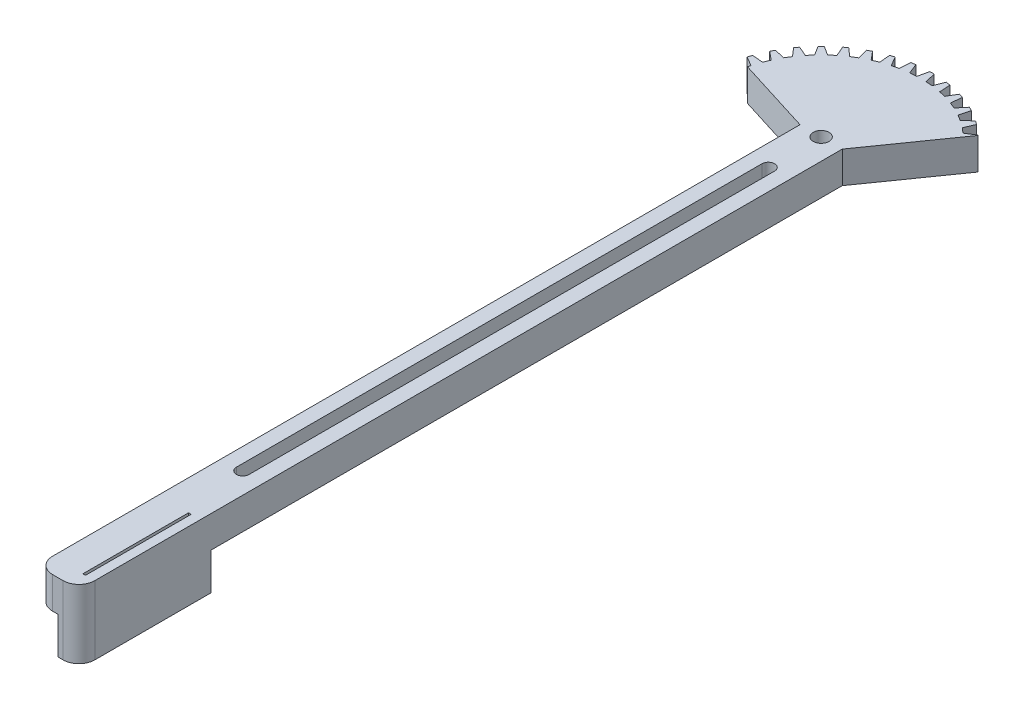
SolidWorks part; units mm, degrees
material "PBT General Purpose"
ref_plane "Front Plane" through (0, 0, 0) normal (0, 0, 1) x (1, 0, 0)
ref_plane "Top Plane" through (0, 0, 0) normal (0, 1, 0) x (1, 0, 0)
ref_plane "Right Plane" through (0, 0, 0) normal (1, 0, 0) x (0, 0, -1)
sketch "Sketch1" plane through (0, 0, 0) normal (0, 1, 0) x (1, 0, 0)
  circle A0 centre (0, 0) radius 21
  circle A1 centre (0, 0) radius 1.5
  dimension "D2" = 3
  dimension "D1" = 42
extrude "Boss-Extrude1" add sketch "Sketch1" along normal blind 6
sketch "Sketch2" plane through (0, 6, 0) normal (0, 1, 0) x (1, 0, 0)
  line L0 (0, 0) -> (0, 15.5) construction
  line L1 (0, 0) -> (-0.4123, 20.996) construction
  line L2 (0, 0) -> (-0.8702, 18.9801) construction
  line L3 (0, 0) -> (-1.4907, 18.9414) construction
  line L4 (-0.8702, 18.9801) -> (-0.4123, 20.996)
  line L5 (0.8702, 18.9801) -> (0.4123, 20.996)
  line L6 (-1.4907, 18.9414) -> (-1.7314, 22)
  line L7 (1.4907, 18.9414) -> (1.7314, 22)
  line L8 (-1.7314, 22) -> (1.7314, 22)
  arc A0 (-0.8702, 18.9801) -> (-1.4907, 18.9414) centre (0, 0) ccw
  circle A1 centre (0, 0) radius 21 construction
  arc A2 (0.4123, 20.996) -> (-0.4123, 20.996) centre (0, 0) ccw
  arc A3 (0.8702, 18.9801) -> (1.4907, 18.9414) centre (0, 0) cw
  dimension "D1" = 19
  dimension "D2" = 1.125
  dimension "D3" = 1.5
  dimension "D4" = 1.875
  dimension "D5" = 22
extrude "Cut-Extrude1" cut sketch "Sketch2" against normal up to next (6 mm away)
pattern_circular "CirPattern1" count 40 over 360 about axis through (0, 0, 0) along (0, 1, 0) of "Cut-Extrude1"
sketch "Sketch3" plane through (0, 6, 0) normal (0, 1, 0) x (1, 0, 0)
  line L0 (4, 0) -> (-4, 0) construction
  line L1 (0, 0) -> (0, 21.0096) construction
  line L2 (0, 0) -> (-26.0972, 6.5552) construction
  line L3 (-4, 0) -> (-20.3673, 5.1159)
  line L4 (-4, 0) -> (4, 0)
  line L6 (0, 0) -> (-7.8504, 27.559) construction
  line L7 (0, 0) -> (15.7913, 16.2954) construction
  line L8 (4, 0) -> (14.6142, 15.0807)
  arc A0 (-20.3673, 5.1159) -> (14.6142, 15.0807) centre (0, 0) ccw
  point P5 (0, 0)
  dimension "D3" = 21
  dimension "D1" = 8
  dimension "D2" = 60
  dimension "D4" = 15.9
  dimension "D5" = 120
extrude "Cut-Extrude2" cut sketch "Sketch3" against normal up to next
sketch "Sketch4" plane through (0, 0, 0) normal (0, -1, 0) x (1, 0, 0)
  line L0 (1.5, 0) -> (4, 0)
  line L1 (-4, 0) -> (-1.5, 0)
  line L2 (-4, 0) -> (-4, 141.5)
  line L3 (-1, 144.5) -> (1, 144.5)
  line L4 (4, 0) -> (4, 141.5)
  arc A0 (1.5, 0) -> (-1.5, 0) centre (0, 0) ccw
  arc A1 (-4, 141.5) -> (-1, 144.5) centre (-1, 141.5) cw
  arc A2 (1, 144.5) -> (4, 141.5) centre (1, 141.5) cw
  point P5 (0, 140)
  point P12 (0, 140)
  point P14 (0, 140)
  dimension "D5" = 3
  dimension "D1" = 4.5
  dimension "D3" = 140
extrude "Boss-Extrude2" add sketch "Sketch4" against normal up to surface (6 mm away) up to face at (-4.0836, 6, -14.6127)
sketch "Sketch5" plane through (0, 0, 0) normal (0, -1, 0) x (1, 0, 0)
  line L0 (-4, 119.5) -> (4, 119.5)
  line L1 (0, 119.5) -> (0, 144.5)
  line L32 (14.6142, -15.0807) -> (4, 0)
  line L33 (4, 0) -> (4, 141.5)
  line L34 (4, 0) -> (4, 141.5)
  line L35 (1, 144.5) -> (-1, 144.5)
  line L36 (-4, 0) -> (-18.455, -4.5182)
  line L37 (-18.32, -5.0376) -> (-20.0957, -6.096)
  line L38 (-19.8409, -6.8802) -> (-17.7822, -6.6928)
  line L39 (-17.3064, -7.8414) -> (-18.8947, -9.1646)
  line L40 (-18.5203, -9.8993) -> (-16.5163, -9.3921)
  line L41 (-15.8667, -10.4522) -> (-17.2284, -12.0075)
  line L42 (-16.7437, -12.6747) -> (-14.8437, -11.8602)
  line L43 (-14.0362, -12.8056) -> (-15.1379, -14.5548)
  line L44 (-14.5548, -15.1379) -> (-12.8056, -14.0362)
  line L45 (-11.8602, -14.8437) -> (-12.6747, -16.7437)
  line L46 (-12.0075, -17.2284) -> (-10.4522, -15.8667)
  line L47 (-9.3921, -16.5163) -> (-9.8993, -18.5203)
  line L48 (-9.1646, -18.8947) -> (-7.8414, -17.3064)
  line L49 (-6.6928, -17.7822) -> (-6.8802, -19.8409)
  line L50 (-6.096, -20.0957) -> (-5.0376, -18.32)
  line L51 (-3.8286, -18.6103) -> (-3.6917, -20.673)
  line L52 (-2.8773, -20.802) -> (-2.1097, -18.8825)
  line L53 (-0.8702, -18.9801) -> (-0.4123, -20.996)
  line L54 (0.4123, -20.996) -> (0.8702, -18.9801)
  line L55 (2.1097, -18.8825) -> (2.8773, -20.802)
  line L56 (3.6917, -20.673) -> (3.8286, -18.6103)
  line L57 (5.0376, -18.32) -> (6.096, -20.0957)
  line L58 (6.8802, -19.8409) -> (6.6928, -17.7822)
  line L59 (7.8414, -17.3064) -> (9.1646, -18.8947)
  line L60 (9.8993, -18.5203) -> (9.3921, -16.5163)
  line L61 (10.4522, -15.8667) -> (12.0075, -17.2284)
  line L62 (12.6747, -16.7437) -> (11.8602, -14.8437)
  line L63 (12.8056, -14.0362) -> (14.5548, -15.1379)
  line L97 (1, 144.5) -> (-1, 144.5)
  line L99 (-4, 141.5) -> (-4, 0)
  line L100 (-4, 141.5) -> (-4, 0)
  arc A28 (4, 141.5) -> (1, 144.5) centre (1, 141.5) ccw
  arc A29 (4, 141.5) -> (1, 144.5) centre (1, 141.5) ccw
  arc A31 (-20.0957, -6.096) -> (-19.8409, -6.8802) centre (0, 0) ccw
  arc A32 (-17.7822, -6.6928) -> (-17.3064, -7.8414) centre (0, 0) ccw
  arc A33 (-18.8947, -9.1646) -> (-18.5203, -9.8993) centre (0, 0) ccw
  arc A34 (-16.5163, -9.3921) -> (-15.8667, -10.4522) centre (0, 0) ccw
  arc A35 (-17.2284, -12.0075) -> (-16.7437, -12.6747) centre (0, 0) ccw
  arc A36 (-14.8437, -11.8602) -> (-14.0362, -12.8056) centre (0, 0) ccw
  arc A37 (-15.1379, -14.5548) -> (-14.5548, -15.1379) centre (0, 0) ccw
  arc A38 (-12.8056, -14.0362) -> (-11.8602, -14.8437) centre (0, 0) ccw
  arc A39 (-12.6747, -16.7437) -> (-12.0075, -17.2284) centre (0, 0) ccw
  arc A40 (-10.4522, -15.8667) -> (-9.3921, -16.5163) centre (0, 0) ccw
  arc A41 (-9.8993, -18.5203) -> (-9.1646, -18.8947) centre (0, 0) ccw
  arc A42 (-7.8414, -17.3064) -> (-6.6928, -17.7822) centre (0, 0) ccw
  arc A43 (-6.8802, -19.8409) -> (-6.096, -20.0957) centre (0, 0) ccw
  arc A44 (-5.0376, -18.32) -> (-3.8286, -18.6103) centre (0, 0) ccw
  arc A45 (-3.6917, -20.673) -> (-2.8773, -20.802) centre (0, 0) ccw
  arc A46 (-2.1097, -18.8825) -> (-0.8702, -18.9801) centre (0, 0) ccw
  arc A47 (-0.4123, -20.996) -> (0.4123, -20.996) centre (0, 0) ccw
  arc A48 (0.8702, -18.9801) -> (2.1097, -18.8825) centre (0, 0) ccw
  arc A49 (2.8773, -20.802) -> (3.6917, -20.673) centre (0, 0) ccw
  arc A50 (3.8286, -18.6103) -> (5.0376, -18.32) centre (0, 0) ccw
  arc A51 (6.096, -20.0957) -> (6.8802, -19.8409) centre (0, 0) ccw
  arc A52 (6.6928, -17.7822) -> (7.8414, -17.3064) centre (0, 0) ccw
  arc A53 (9.1646, -18.8947) -> (9.8993, -18.5203) centre (0, 0) ccw
  arc A54 (9.3921, -16.5163) -> (10.4522, -15.8667) centre (0, 0) ccw
  arc A55 (12.0075, -17.2284) -> (12.6747, -16.7437) centre (0, 0) ccw
  arc A56 (11.8602, -14.8437) -> (12.8056, -14.0362) centre (0, 0) ccw
  arc A57 (14.5548, -15.1379) -> (14.6142, -15.0807) centre (0, 0) ccw
  arc A87 (-1, 144.5) -> (-4, 141.5) centre (-1, 141.5) ccw
  arc A88 (-1, 144.5) -> (-4, 141.5) centre (-1, 141.5) ccw
  arc A90 (-18.455, -4.5182) -> (-18.32, -5.0376) centre (0, 0) ccw
  arc A91 (-18.455, -4.5182) -> (-18.32, -5.0376) centre (0, 0) ccw
  dimension "D2" = 25
  dimension "D1" = 0
extrude "Boss-Extrude3" add sketch "Sketch5" along normal blind 7 contours L34 A29 L97 L1 L0
sketch "Sketch7" plane through (0, -7, 0) normal (0, -1, 0) x (1, 0, 0)
  line L5 (0, 119.5) -> (4, 119.5) construction
  line L7 (1.75, 121.5) -> (2.25, 121.5)
  line L8 (1.75, 121.5) -> (1.75, 141.5)
  line L9 (1.75, 141.5) -> (2.25, 141.5)
  line L10 (2.25, 121.5) -> (2.25, 141.5)
  point P4 (2, 121.5)
  point P10 (2, 119.5)
  dimension "D1" = 2
  dimension "D2" = 0.5
  dimension "D3" = 20
extrude "Cut-Extrude4" cut sketch "Sketch7" against normal up to next
sketch "Sketch8" plane through (0, 0, 0) normal (0, -1, 0) x (1, 0, 0)
  line L0 (0, 10) -> (0, 109.5) construction
  line L1 (-1.2, 10) -> (-1.2, 109.5)
  line L2 (1.2, 10) -> (1.2, 109.5)
  line L3 (0, 119.5) -> (4, 119.5) construction
  arc A0 (-1.2, 10) -> (1.2, 10) centre (0, 10) ccw
  arc A1 (1.2, 109.5) -> (-1.2, 109.5) centre (0, 109.5) ccw
  point P3 (0, 59.75)
  dimension "D2" = 1.2
  dimension "D1" = 10
  dimension "D3" = 10
extrude "Cut-Extrude5" cut sketch "Sketch8" against normal up to next
equation "\"num_teeth\"= 40"
equation "\"D2@Sketch2\"=(1.5/6)*(360 / \"num_teeth\")*0.5"
equation "\"D3@Sketch2\"=(2/6)*(360 / \"num_teeth\")*0.5"
equation "\"D4@Sketch2\"=(2.5/6)*(360 / \"num_teeth\")*0.5"
equation "\"D1@CirPattern1\"=\"num_teeth\""
equation "\"teeth_angle_offset\"= 15.9deg"
equation "\"D4@Sketch3\"=\"teeth_angle_offset\""
equation "\"diameter\"= 40mm"
equation "\"D1@Sketch1\"=\"diameter\" + 2"
equation "\"D1@Sketch2\"=(\"diameter\" / 2) - 1"
equation "\"D3@Sketch3\"=(\"diameter\" / 2) + 1"
equation "\"teeth_fraction_required\"= 1 / 3"
equation "\"D5@Sketch3\"=360 * \"teeth_fraction_required\""
equation "\"D2@Sketch3\"=360 * \"teeth_fraction_required\" * 0.5"
equation "\"bar_length\"= 140mm"
equation "\"D3@Sketch4\"=\"bar_length\""
equation "\"D5@Sketch2\"=\"diameter\" / 2 + 2"
